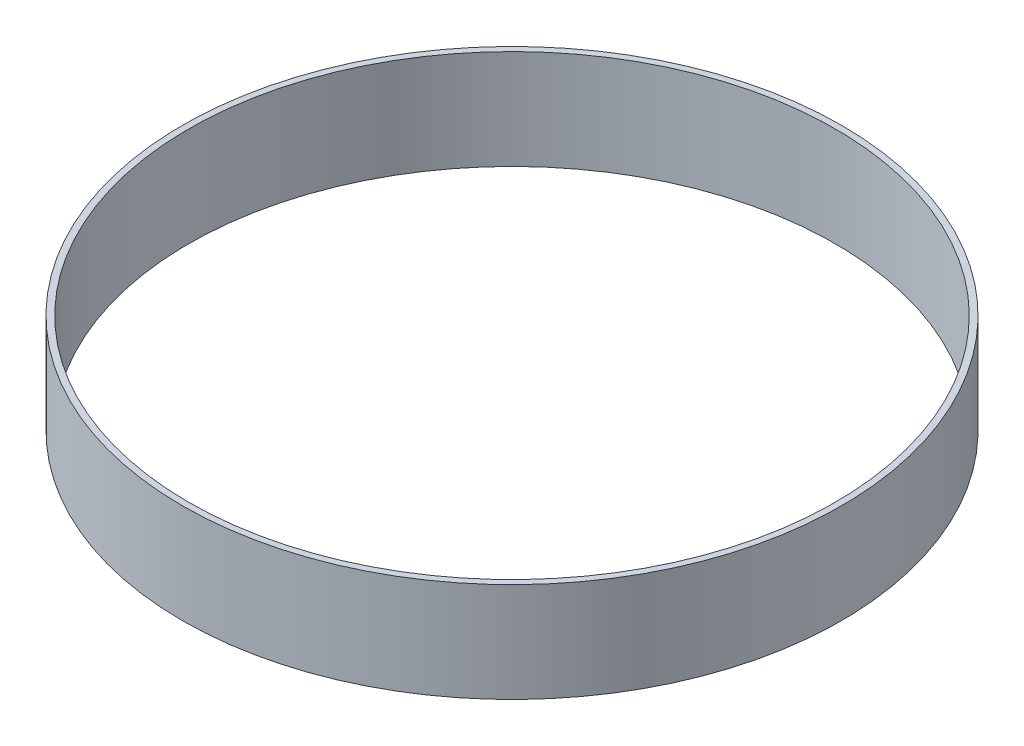
SolidWorks part; units mm, degrees
material "ABS PC"
ref_plane "Front" through (0, 0, 0) normal (0, 0, 1) x (1, 0, 0)
ref_plane "Top" through (0, 0, 0) normal (0, 1, 0) x (1, 0, 0)
ref_plane "Right" through (0, 0, 0) normal (1, 0, 0) x (0, 0, -1)
sketch "Sketch1" plane through (0, 0, 0) normal (0, 1, 0) x (1, 0, 0)
  circle A0 centre (0, 0) radius 130
  circle A1 centre (0, 0) radius 132.5
  dimension "D1" = 2.5
  dimension "D2" = 260
extrude "Boss-Extrude1" add sketch "Sketch1" along normal blind 40
sketch "Sketch2" plane through (0, 0, 0) normal (0, 0, 1) x (1, 0, 0)
  line L0 (0, 0) -> (0, 5) construction
  circle A0 centre (0, 5) radius 2.5
  dimension "D2" = 5
  dimension "D1" = 5
